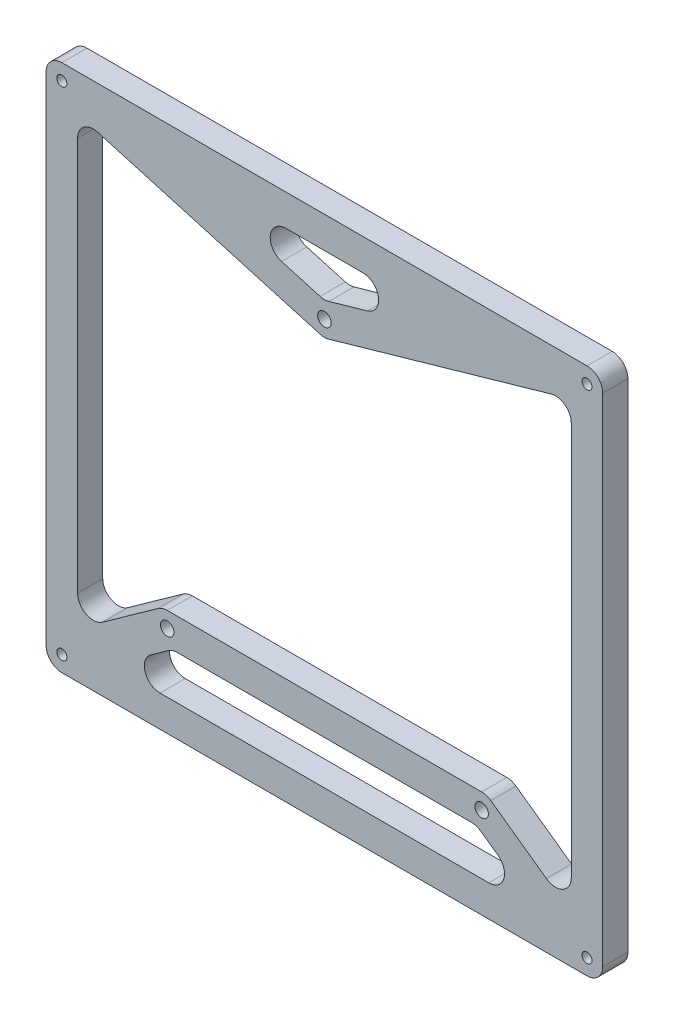
SolidWorks part; units mm, degrees
ref_plane "Plan de face" through (0, 0, 0) normal (0, 0, 1) x (1, 0, 0)
ref_plane "Plan de dessus" through (0, 0, 0) normal (0, 1, 0) x (1, 0, 0)
ref_plane "Plan de droite" through (0, 0, 0) normal (1, 0, 0) x (0, 0, -1)
sketch "Esquisse1" plane through (0, 0, 0) normal (0, 0, 1) x (1, 0, 0)
  line L0 (0, 55.0931) -> (-50, -55.0931) construction
  line L5 (-83.5, -79) -> (83.5, -79) construction
  line L6 (-83.5, -79) -> (-83.5, 79) construction
  line L7 (-83.5, 79) -> (83.5, 79) construction
  line L8 (83.5, -79) -> (83.5, 79) construction
  line L9 (-83.5, -79) -> (83.5, 79) construction
  line L10 (-83.5, 79) -> (83.5, -79) construction
  line L11 (-50, -55.0931) -> (50, -55.0931) construction
  line L12 (50, -55.0931) -> (0, 55.0931) construction
  line L13 (0, 55.0931) -> (0, -55.0931) construction
  line L14 (-83.5, 79) -> (0, 55.0931) construction
  line L15 (0, 55.0931) -> (83.5, 79) construction
  line L17 (-50, -55.0931) -> (-83.5, -79) construction
  line L19 (50, -55.0931) -> (83.5, -79) construction
  line L21 (-52.9044, -51.0232) -> (-70.5956, -63.6482)
  line L22 (-83.5, -84) -> (83.5, -84)
  line L23 (52.9044, -51.0232) -> (70.5956, -63.6482)
  line L24 (-50, -50.0931) -> (50, -50.0931)
  line L25 (-49.7022, -61.0232) -> (-55.1768, -64.9301)
  line L26 (-52.2723, -74) -> (52.2723, -74)
  line L27 (49.7022, -61.0232) -> (55.1768, -64.9301)
  line L28 (-46.7977, -60.0931) -> (46.7977, -60.0931)
  line L29 (-72.1237, 70.542) -> (-1.3763, 50.2862)
  line L30 (1.3763, 50.2862) -> (72.1237, 70.542)
  line L31 (-83.5, 84) -> (83.5, 84)
  line L32 (-13.6186, 64.1931) -> (-1.3763, 60.688)
  line L33 (1.3763, 60.688) -> (13.6186, 64.1931)
  line L34 (-12.2423, 74) -> (12.2423, 74)
  line L36 (88.5, -79) -> (88.5, 79)
  line L37 (-88.5, -79) -> (-88.5, 79)
  line L39 (-78.5, -59.5783) -> (-78.5, 65.7351)
  line L40 (-119.1288, 84) -> (119.1288, 84) construction
  line L41 (-119.1288, 84) -> (0, 49.8922) construction
  line L42 (0, 49.8922) -> (119.1288, 84) construction
  line L43 (78.5, -59.5783) -> (78.5, 65.7351)
  line L44 (-47.8712, 74) -> (0, 60.294) construction
  line L45 (-51.6011, -50.0931) -> (-99.1138, -84) construction
  line L46 (-99.1138, -84) -> (99.1138, -84) construction
  line L47 (51.6011, -50.0931) -> (99.1138, -84) construction
  line L48 (-47.8712, 74) -> (47.8712, 74) construction
  line L49 (0, 60.294) -> (47.8712, 74) construction
  line L50 (-67.8862, -74) -> (67.8862, -74) construction
  line L51 (48.3989, -60.0931) -> (67.8862, -74) construction
  line L52 (-48.3989, -60.0931) -> (-67.8862, -74) construction
  line L53 (-48.3989, -60.0931) -> (48.3989, -60.0931) construction
  line L54 (-51.6011, -50.0931) -> (51.6011, -50.0931) construction
  arc A0 (-83.5, -84) -> (-88.5, -79) centre (-83.5, -79) cw
  arc A1 (-83.5, 84) -> (-88.5, 79) centre (-83.5, 79) ccw
  arc A2 (88.5, -79) -> (83.5, -84) centre (83.5, -79) cw
  arc A3 (88.5, 79) -> (83.5, 84) centre (83.5, 79) ccw
  arc A4 (-13.6186, 64.1931) -> (-12.2423, 74) centre (-12.2423, 69) cw
  arc A5 (13.6186, 64.1931) -> (12.2423, 74) centre (12.2423, 69) ccw
  arc A6 (52.2723, -74) -> (55.1768, -64.9301) centre (52.2723, -69) ccw
  arc A7 (-55.1768, -64.9301) -> (-52.2723, -74) centre (-52.2723, -69) ccw
  arc A8 (49.7022, -61.0232) -> (46.7977, -60.0931) centre (46.7977, -65.0931) ccw
  arc A9 (-49.7022, -61.0232) -> (-46.7977, -60.0931) centre (-46.7977, -65.0931) cw
  arc A10 (-70.5956, -63.6482) -> (-78.5, -59.5783) centre (-73.5, -59.5783) cw
  arc A11 (-52.9044, -51.0232) -> (-50, -50.0931) centre (-50, -55.0931) cw
  arc A12 (52.9044, -51.0232) -> (50, -50.0931) centre (50, -55.0931) ccw
  arc A13 (78.5, -59.5783) -> (70.5956, -63.6482) centre (73.5, -59.5783) cw
  arc A14 (78.5, 65.7351) -> (72.1237, 70.542) centre (73.5, 65.7351) ccw
  arc A15 (-1.3763, 60.688) -> (1.3763, 60.688) centre (0, 65.4949) ccw
  arc A16 (-1.3763, 50.2862) -> (1.3763, 50.2862) centre (0, 55.0931) ccw
  arc A17 (-72.1237, 70.542) -> (-78.5, 65.7351) centre (-73.5, 65.7351) ccw
  point P0 (0, 0)
  point P11 (-83.5, 74)
  point P14 (83.5, 74)
  point P17 (78.5, 79)
  point P18 (78.5, -79)
  point P19 (0, 0)
  point P21 (-79.8756, -82.4444)
  point P22 (-46.3756, -47.193)
  point P23 (-50, -48.7487)
  point P24 (50, -48.7487)
  point P25 (46.3756, -47.193)
  point P26 (79.8756, -82.4444)
  point P27 (-4.5531, 68.5037)
  point P28 (-54.5531, -41.6826)
  point P29 (54.5531, -41.6826)
  point P30 (4.5531, 68.5037)
  point P31 (0.7439, 61.4932)
  point P32 (84.2439, 74.0556)
  point P33 (-84.2439, 74.0556)
  point P34 (-0.7439, 61.4932)
  point P37 (-78.5, 79)
  point P38 (-78.5, -79)
  point P41 (-83.5, -74)
  point P42 (83.5, -74)
  point P43 (-87.1244, -75.5556)
  point P44 (-53.6244, -40.3043)
  point P45 (-50, -38.7487)
  point P46 (50, -38.7487)
  point P47 (53.6244, -40.3043)
  point P48 (87.1244, -75.5556)
  point P49 (4.5531, 64.3714)
  point P50 (-45.4469, -45.8148)
  point P51 (45.4469, -45.8148)
  point P52 (-4.5531, 64.3714)
  point P53 (-0.7439, 71.3819)
  point P54 (82.7561, 83.9444)
  point P55 (-82.7561, 83.9444)
  point P56 (0.7439, 71.3819)
  point P67 (-78.5, -79)
  point P68 (-78.5, 79)
  point P73 (78.5, -79)
  point P74 (78.5, 79)
  point P80 (-78.4179, 71.3819)
  point P85 (0, 0)
  point P86 (-71.8452, -84)
  dimension "D5" = 5
  dimension "D11" = 5
  dimension "D1" = 167
  dimension "D2" = 158
  dimension "D3" = 121
  dimension "D4" = 100
  dimension "D6" = 5
  dimension "D7" = 5
  dimension "D8" = 5
  dimension "D9" = 5
  dimension "D10" = 5
extrude "Boss.-Extru.1" add sketch "Esquisse1" along normal blind 8
hole_wizard "Dégagement M31" positions "Esquisse5" profile "Esquisse6" hole size "M3" standard "ISO" end condition through all
sketch "Esquisse5" plane through (0, 0, 8) normal (0, 0, 1) x (1, 0, 0)
  point P13 (-83.5, 79)
  point P16 (-83.5, -79)
  point P19 (83.5, -79)
  point P22 (83.5, 79)
sketch "Esquisse6" plane through (-83.5, 79, 8) normal (1, 0, 0) x (0, -1, 0)
  line L0 (0, 0) -> (0, 8)
  line L1 (0, 8) -> (1.6, 8)
  line L2 (1.6, 8) -> (1.6, 0)
  line L5 (1.6, 0) -> (0, 0)
  line L11 (0, -6.35) -> (0, 107.95) construction
  dimension "Diamètre du perçage jusqu'au prochain" = 3.2
  dimension "Profondeur du perçage jusqu'au prochain" = 8
hole_wizard "Dégagement M41" positions "Esquisse7" profile "Esquisse8" hole size "M4" standard "ISO" end condition through all
sketch "Esquisse7" plane through (0, 0, 8) normal (0, 0, 1) x (1, 0, 0)
  point P10 (-50, -55.0931)
  point P13 (50, -55.0931)
  point P16 (0, 55.0931)
sketch "Esquisse8" plane through (-50, -55.0931, 8) normal (1, 0, 0) x (0, -1, 0)
  line L0 (0, 0) -> (0, 8)
  line L1 (0, 8) -> (2.15, 8)
  line L2 (2.15, 8) -> (2.15, 0)
  line L5 (2.15, 0) -> (0, 0)
  line L11 (0, -6.35) -> (0, 107.95) construction
  dimension "Diamètre du perçage jusqu'au prochain" = 4.3
  dimension "Profondeur du perçage jusqu'au prochain" = 8
